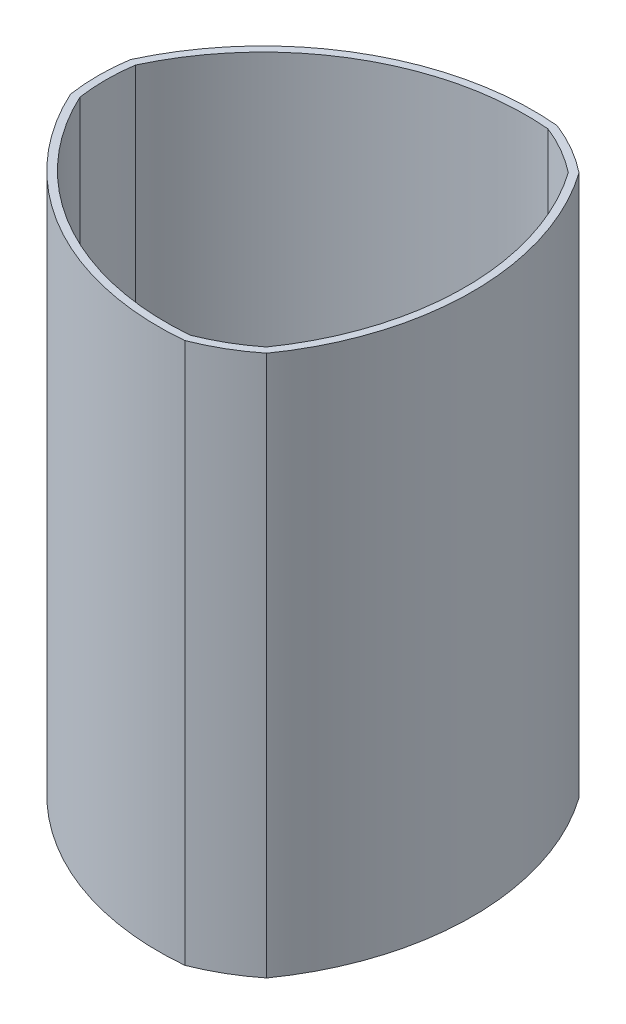
SolidWorks part; units mm, degrees
ref_plane "Front Plane" through (0, 0, 0) normal (0, 0, 1) x (1, 0, 0)
ref_plane "Top Plane" through (0, 0, 0) normal (0, 1, 0) x (1, 0, 0)
ref_plane "Right Plane" through (0, 0, 0) normal (1, 0, 0) x (0, 0, -1)
sketch "Circle :)" plane through (0, 0, 0) normal (0, 1, 0) x (1, 0, 0)
  circle A3 centre (0, 0) radius 84.455
  dimension "D1" = 168.91
sketch "Sketch3" plane through (0, 0, 0) normal (0, 1, 0) x (1, 0, 0)
  line L0 (-106.5987, 0) -> (106.5987, 0) construction
  arc A0 (-83.5001, 12.6641) -> (-83.5001, -12.6641) centre (0, 0) ccw
  arc A8 (52.7174, 65.9812) -> (30.7827, 78.6452) centre (0, 0) ccw
  arc A9 (30.7827, -78.6452) -> (52.7174, -65.9812) centre (0, 0) ccw
  arc A10 (-83.5001, 12.6641) -> (30.7827, 78.6452) centre (20.3076, -35.1737) cw
  arc A11 (52.7174, 65.9812) -> (52.7174, -65.9812) centre (-40.6151, 0) cw
  arc A12 (30.7827, -78.6452) -> (-83.5001, -12.6641) centre (20.3076, 35.1737) cw
  arc A13 (50.3844, 63.7797) -> (50.3844, -63.7797) centre (-40.6151, 0) cw
  arc A14 (30.0427, -75.524) -> (50.3844, -63.7797) centre (0, 0) ccw
  arc A15 (30.0427, -75.524) -> (-80.427, -11.7443) centre (20.3076, 35.1737) cw
  arc A16 (-80.427, 11.7443) -> (-80.427, -11.7443) centre (0, 0) ccw
  arc A17 (-80.427, 11.7443) -> (30.0427, 75.524) centre (20.3076, -35.1737) cw
  arc A18 (50.3844, 63.7797) -> (30.0427, 75.524) centre (0, 0) ccw
  dimension "D1" = 84.455
  dimension "D4" = 114.3
  dimension "D5" = 3.175
  dimension "D2" = 3
  dimension "D3" = 3
extrude "Sides (the gap value can be changed)" add sketch "Sketch3" along normal blind 228.6
sketch "Sketch7" plane through (0, 0, 0) normal (0, 1, 0) x (1, 0, 0)
  arc A0 (50.3844, 63.7797) -> (30.0427, 75.524) centre (0, 0) ccw construction
  arc A1 (50.3844, -63.7797) -> (50.3844, 63.7797) centre (-40.6151, 0) ccw construction
  arc A2 (30.0427, -75.524) -> (50.3844, -63.7797) centre (0, 0) ccw construction
  arc A3 (-80.427, -11.7443) -> (30.0427, -75.524) centre (20.3076, 35.1737) ccw construction
  arc A4 (-80.427, 11.7443) -> (-80.427, -11.7443) centre (0, 0) ccw construction
  arc A5 (30.0427, 75.524) -> (-80.427, 11.7443) centre (20.3076, -35.1737) ccw construction
  arc A6 (50.3844, 63.7797) -> (30.0427, 75.524) centre (0, 0) ccw
  arc A7 (50.3844, -63.7797) -> (50.3844, 63.7797) centre (-40.6151, 0) ccw
  arc A8 (30.0427, -75.524) -> (50.3844, -63.7797) centre (0, 0) ccw
  arc A9 (-80.427, -11.7443) -> (30.0427, -75.524) centre (20.3076, 35.1737) ccw
  arc A10 (-80.427, 11.7443) -> (-80.427, -11.7443) centre (0, 0) ccw
  arc A11 (30.0427, 75.524) -> (-80.427, 11.7443) centre (20.3076, -35.1737) ccw
extrude "base" add sketch "Sketch7" along normal blind 3.175
sketch "Sketch8" plane through (0, 3.175, 0) normal (0, 1, 0) x (1, 0, 0)
  line L0 (6.604, -46.2915) -> (6.604, 44.7675) construction
  line L1 (-6.604, 44.7675) -> (6.604, 44.7675)
  line L2 (-6.604, 44.7675) -> (-6.604, 43.2435)
  line L3 (-6.604, 43.2435) -> (6.604, 43.2435)
  line L4 (6.604, 44.7675) -> (6.604, 43.2435)
  line L5 (-6.604, -44.7675) -> (6.604, -44.7675)
  line L6 (-6.604, -44.7675) -> (-6.604, -46.2915)
  line L7 (-6.604, -46.2915) -> (6.604, -46.2915)
  line L8 (6.604, -44.7675) -> (6.604, -46.2915)
  circle A0 centre (0, 0) radius 84.455 construction
  point P10 (0, 0)
  dimension "D1" = 1.524
  dimension "D2" = 13.208
  dimension "D3" = 1.524
  dimension "D4" = 13.208
  dimension "D5" = 88.011
  dimension "D6" = 44.7675
  dimension "D7" = 6.604
extrude "Shock cord cuts(Can be moved, current dim arbitrary)" cut sketch "Sketch8" against normal through all
equation "\"D1@Sketch3\"=6.65/2"
equation "\"D5@Sketch8\"=3.525-.06"
equation "\"D6@Sketch8\"=3.525/2"
equation "\"D7@Sketch8\"=.52/2"
